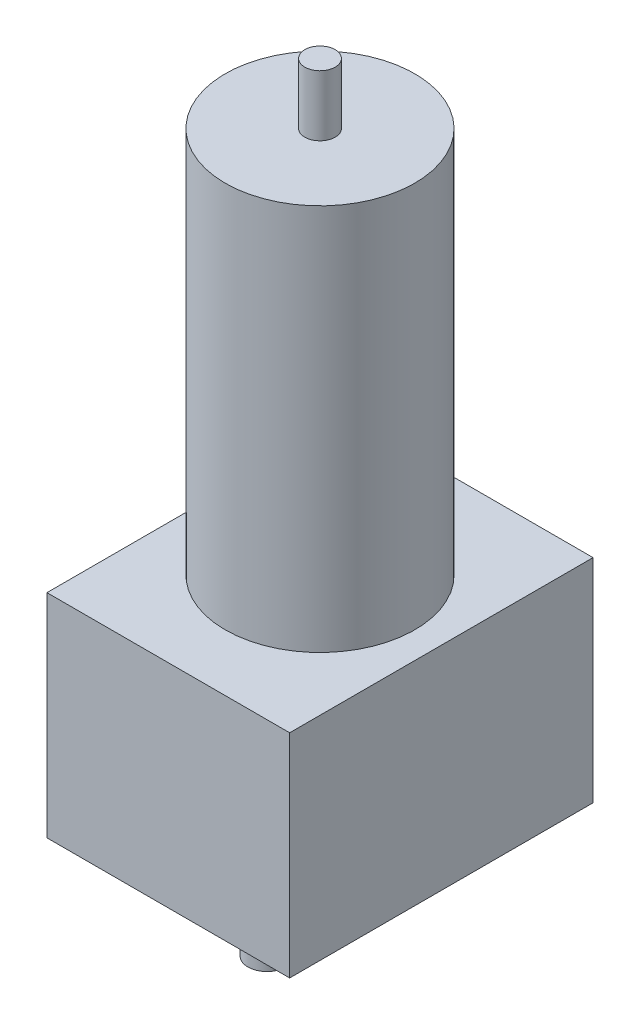
SolidWorks part; units mm, degrees
ref_plane "Front Plane" through (0, 0, 0) normal (0, 0, 1) x (1, 0, 0)
ref_plane "Top Plane" through (0, 0, 0) normal (0, 1, 0) x (1, 0, 0)
ref_plane "Right Plane" through (0, 0, 0) normal (1, 0, 0) x (0, 0, -1)
sketch "Sketch1" plane through (0, 0, 0) normal (0, 1, 0) x (1, 0, 0)
  line L1 (-50.8, 63.5) -> (50.8, 63.5)
  line L2 (-50.8, 63.5) -> (-50.8, -63.5)
  line L3 (-50.8, -63.5) -> (50.8, -63.5)
  line L4 (50.8, 63.5) -> (50.8, -63.5)
  line L5 (-50.8, 63.5) -> (50.8, -63.5) construction
  line L6 (-50.8, -63.5) -> (50.8, 63.5) construction
  point P0 (0, 0)
  dimension "D1" = 127
  dimension "D2" = 101.6
extrude "Boss-Extrude2" add sketch "Sketch1" along normal blind 88.9
sketch "Sketch3" plane through (0, 88.9, 0) normal (0, 1, 0) x (1, 0, 0)
  circle A0 centre (0, 0) radius 39.6875
  dimension "D1" = 79.375
extrude "Boss-Extrude3" add sketch "Sketch3" along normal blind 161.925
sketch "Sketch4" plane through (0, 250.825, 0) normal (0, 1, 0) x (1, 0, 0)
  circle A0 centre (0, 0) radius 6.35
  dimension "D1" = 12.7
extrude "Boss-Extrude4" add sketch "Sketch4" along normal blind 25.4
sketch "Sketch5" plane through (0, 0, 0) normal (0, -1, 0) x (-1, 0, 0)
  line L0 (0, -63.5) -> (0, 63.5) construction
  line L3 (50.8, -63.5) -> (-50.8, -63.5) construction
  line L4 (-50.8, 63.5) -> (50.8, 63.5) construction
  circle A0 centre (0, -22.225) radius 7.9375
  dimension "D1" = 15.875
  dimension "D2" = 41.275
extrude "Boss-Extrude5" add sketch "Sketch5" along normal blind 38.1
sketch "Sketch6" plane through (0, 0, 0) normal (0, -1, 0) x (-1, 0, 0)
  line L0 (-42.8625, -63.5) -> (-42.8625, 63.5) construction
  line L1 (42.8625, -63.5) -> (42.8625, 63.5) construction
  line L2 (50.8, -63.5) -> (-50.8, -63.5) construction
  line L3 (-50.8, 63.5) -> (50.8, 63.5) construction
  circle A0 centre (42.8625, -38.1) radius 3.9687
  circle A1 centre (-42.8625, -38.1) radius 3.9687
  circle A2 centre (42.8625, 50.1741) radius 3.9687
  circle A3 centre (-42.8625, 50.1741) radius 3.9687
  dimension "D4" = 7.9375
  dimension "D5" = 7.9375
  dimension "D8" = 7.9375
  dimension "D1" = 7.9375
  dimension "D2" = 7.9375
  dimension "D3" = 25.4
  dimension "D6" = 25.4
  dimension "D7" = 13.3259
extrude "Cut-Extrude1" cut sketch "Sketch6" against normal blind 25.4
